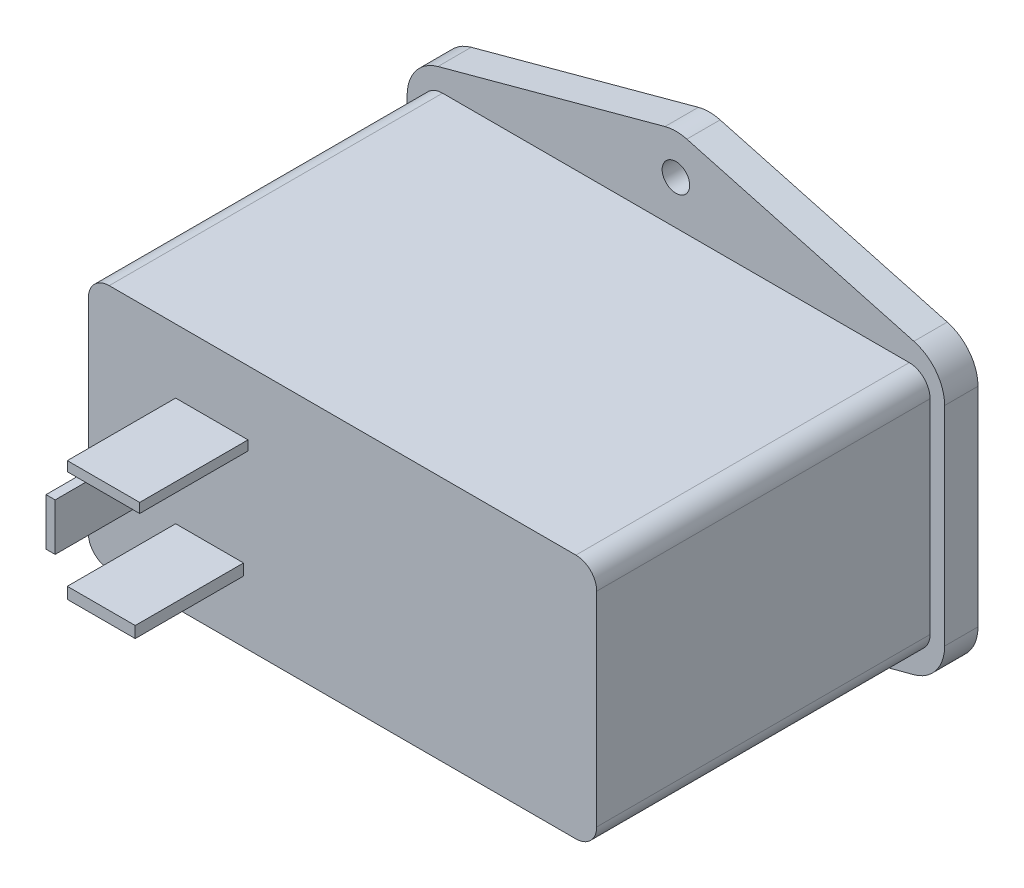
SolidWorks part; units mm, degrees
ref_plane "Front Plane" through (0, 0, 0) normal (0, 0, 1) x (1, 0, 0)
ref_plane "Top Plane" through (0, 0, 0) normal (0, 1, 0) x (1, 0, 0)
ref_plane "Right Plane" through (0, 0, 0) normal (1, 0, 0) x (0, 0, -1)
sketch "Sketch1" plane through (0, 0, 0) normal (0, 0, 1) x (1, 0, 0)
  line L1 (2.5, 0) -> (58.5, 0)
  line L2 (0, 2.5) -> (0, 27)
  line L3 (2.5, 29.5) -> (58.5, 29.5)
  line L4 (61, 2.5) -> (61, 27)
  arc A0 (2.5, 0) -> (0, 2.5) centre (2.5, 2.5) cw
  arc A1 (58.5, 0) -> (61, 2.5) centre (58.5, 2.5) ccw
  arc A2 (58.5, 29.5) -> (61, 27) centre (58.5, 27) cw
  arc A3 (0, 27) -> (2.5, 29.5) centre (2.5, 27) cw
  point P7 (0, 0)
  point P10 (61, 0)
  point P15 (0, 29.5)
  dimension "D3" = 2.5
  dimension "D1" = 61
  dimension "D2" = 29.5
extrude "Boss-Extrude1" add sketch "Sketch1" along normal blind 40
sketch "Sketch2" plane through (0, 0, 0) normal (0, 0, -1) x (-1, 0, 0)
  line L0 (0, 14.75) -> (-61, 14.75) construction
  line L1 (0, 27) -> (0, 2.5) construction
  line L2 (-61, 2.5) -> (-61, 27) construction
  line L4 (-29.1922, 39.3793) -> (-1.9422, 31.9945)
  line L6 (-62.75, 2.1686) -> (-62.75, 27.1686)
  line L8 (1.75, 2.1686) -> (1.75, 27.1686)
  line L9 (-62.75, -10.25) -> (1.75, 39.75) construction
  line L10 (-62.75, 39.75) -> (1.75, -10.25) construction
  line L11 (-1.9653, -2.6636) -> (-29.2153, -9.9084)
  line L12 (-31.8078, 39.3793) -> (-59.0578, 31.9945)
  line L13 (-31.7847, -9.9084) -> (-59.0347, -2.6636)
  arc A0 (-59.0347, -2.6636) -> (-62.75, 2.1686) centre (-57.75, 2.1686) cw
  arc A1 (-59.0578, 31.9945) -> (-62.75, 27.1686) centre (-57.75, 27.1686) ccw
  arc A2 (-29.1922, 39.3793) -> (-31.8078, 39.3793) centre (-30.5, 34.5534) ccw
  arc A3 (-29.2153, -9.9084) -> (-31.7847, -9.9084) centre (-30.5, -5.0763) cw
  arc A4 (-1.9653, -2.6636) -> (1.75, 2.1686) centre (-3.25, 2.1686) ccw
  arc A5 (-1.9422, 31.9945) -> (1.75, 27.1686) centre (-3.25, 27.1686) cw
  circle A6 centre (-30.5, 34.75) radius 1.65
  circle A7 centre (-30.5, -5.0763) radius 1.65
  point P8 (-30.5, -5.25)
  point P9 (-30.5, 34.75)
  point P10 (-30.5, 14.75)
  point P29 (-30.5, -10.25)
  dimension "D5" = 5
  dimension "D6" = 3.3
  dimension "D7" = 3.3
  dimension "D10" = 3.6922
  dimension "D3" = 39.6297
  dimension "D4" = 64.5
  dimension "D1" = 20
  dimension "D2" = 20
  dimension "D8" = 25
  dimension "D9" = 25
extrude "Boss-Extrude2" add sketch "Sketch2" along normal blind 4
sketch "Sketch3" plane through (0, 0, 40) normal (0, 0, 1) x (1, 0, 0)
  line L1 (7.914, 11.3181) -> (9.0086, 11.3181)
  line L2 (7.914, 11.3181) -> (7.914, 16.9876)
  line L3 (7.914, 16.9876) -> (9.0086, 16.9876)
  line L4 (9.0086, 11.3181) -> (9.0086, 16.9876)
  line L5 (10.4698, 7.3791) -> (18.6195, 7.3791)
  line L6 (10.4698, 7.3791) -> (10.4698, 8.7415)
  line L7 (10.4698, 8.7415) -> (18.6195, 8.7415)
  line L8 (18.6195, 7.3791) -> (18.6195, 8.7415)
  line L9 (10.4698, 20.6454) -> (19.1556, 20.6454)
  line L10 (10.4698, 20.6454) -> (10.4698, 21.8008)
  line L11 (10.4698, 21.8008) -> (19.1556, 21.8008)
  line L12 (19.1556, 20.6454) -> (19.1556, 21.8008)
extrude "Boss-Extrude3" add sketch "Sketch3" along normal blind 13
